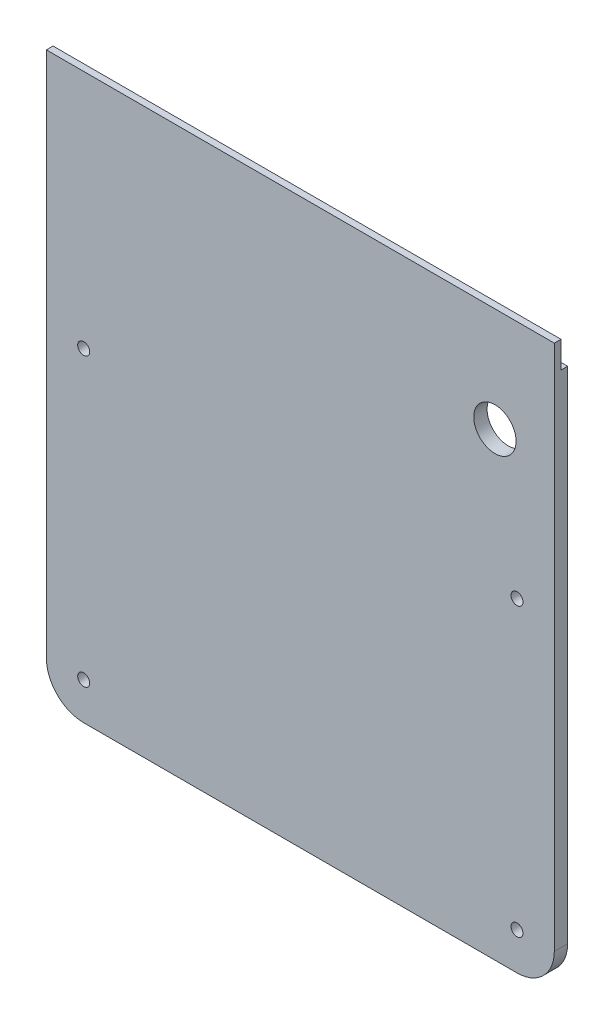
SolidWorks part; units mm, degrees
ref_plane "Front Plane" through (0, 0, 0) normal (0, 0, 1) x (1, 0, 0)
ref_plane "Top Plane" through (0, 0, 0) normal (0, 1, 0) x (1, 0, 0)
ref_plane "Right Plane" through (0, 0, 0) normal (1, 0, 0) x (0, 0, -1)
sketch "Sketch4" plane through (0, 0, 0) normal (0, 0, 1) x (1, 0, 0)
  line L0 (-66.0801, -1201.5626) -> (96.4199, -1201.5626)
  line L1 (-80.0801, -1187.5626) -> (-80.0801, -812.4374)
  line L2 (96.4199, -798.4374) -> (-66.0801, -798.4374)
  line L3 (110.4199, -812.4374) -> (110.4199, -1187.5626)
  circle A0 centre (96.4199, -1187.5626) radius 2.25
  circle A1 centre (-66.0801, -1187.5626) radius 2.25
  circle A2 centre (-66.0801, -1080) radius 2.25
  circle A3 centre (-66.0801, -920) radius 2.25
  circle A4 centre (-66.0801, -812.4374) radius 2.25
  circle A5 centre (96.4199, -812.4374) radius 2.25
  circle A6 centre (96.4199, -920) radius 2.25
  circle A7 centre (96.4199, -1080) radius 2.25
  circle A8 centre (96.4199, -1080) radius 14
  circle A9 centre (96.4199, -1187.5626) radius 14
  circle A10 centre (-66.0801, -1187.5626) radius 14
  circle A11 centre (-66.0801, -1080) radius 14
  circle A12 centre (-66.0801, -920) radius 14
  circle A13 centre (88.1478, -1029.08) radius 7.9375
  circle A14 centre (96.4199, -920) radius 14
  circle A15 centre (96.4199, -812.4374) radius 14
  circle A16 centre (-66.0801, -812.4374) radius 14
  point P0 (96.4199, -1182.7361)
  point P1 (96.4199, -1080)
  point P3 (96.4199, -920)
  point P5 (96.4199, -812.4374)
  point P7 (-66.0801, -812.4374)
  point P9 (-66.0801, -920)
  point P11 (-66.0801, -1080)
  point P13 (-66.0801, -1187.5626)
  dimension "D1" = 28
extrude "Boss-Extrude1" add sketch "Sketch4" along normal blind 5
sketch "Sketch5" plane through (0, 0, 5) normal (0, 0, 1) x (1, 0, 0)
  line L0 (-80.0801, -1000) -> (110.4199, -1000) construction
  line L1 (-80.0801, -1187.5626) -> (-80.0801, -812.4374) construction
  line L2 (110.4199, -812.4374) -> (110.4199, -1187.5626) construction
sketch "Sketch6" plane through (110.4199, 0, 0) normal (1, 0, 0) x (0, 0, -1)
  line L0 (0, -1000) -> (-14.8805, -1000) construction
  line L1 (0, -812.4374) -> (0, -1187.5626) construction
  line L2 (-5, -990) -> (-2.5, -990)
  line L3 (-5, -812.4374) -> (-5, -1187.5626) construction
  line L4 (-2.5, -990) -> (-2.5, -1000)
  line L5 (-2.5, -1000) -> (0, -1000)
  line L6 (0, -1000) -> (102.6882, -812.4374)
  line L7 (102.6882, -812.4374) -> (-56.6415, -690.4639)
  line L8 (-56.6415, -690.4639) -> (-113.6281, -898.2256)
  line L9 (-113.6281, -898.2256) -> (-5, -990)
  dimension "D1" = 10
  dimension "D2" = 2.5
extrude "Cut-Extrude1" cut sketch "Sketch6" against normal through all
